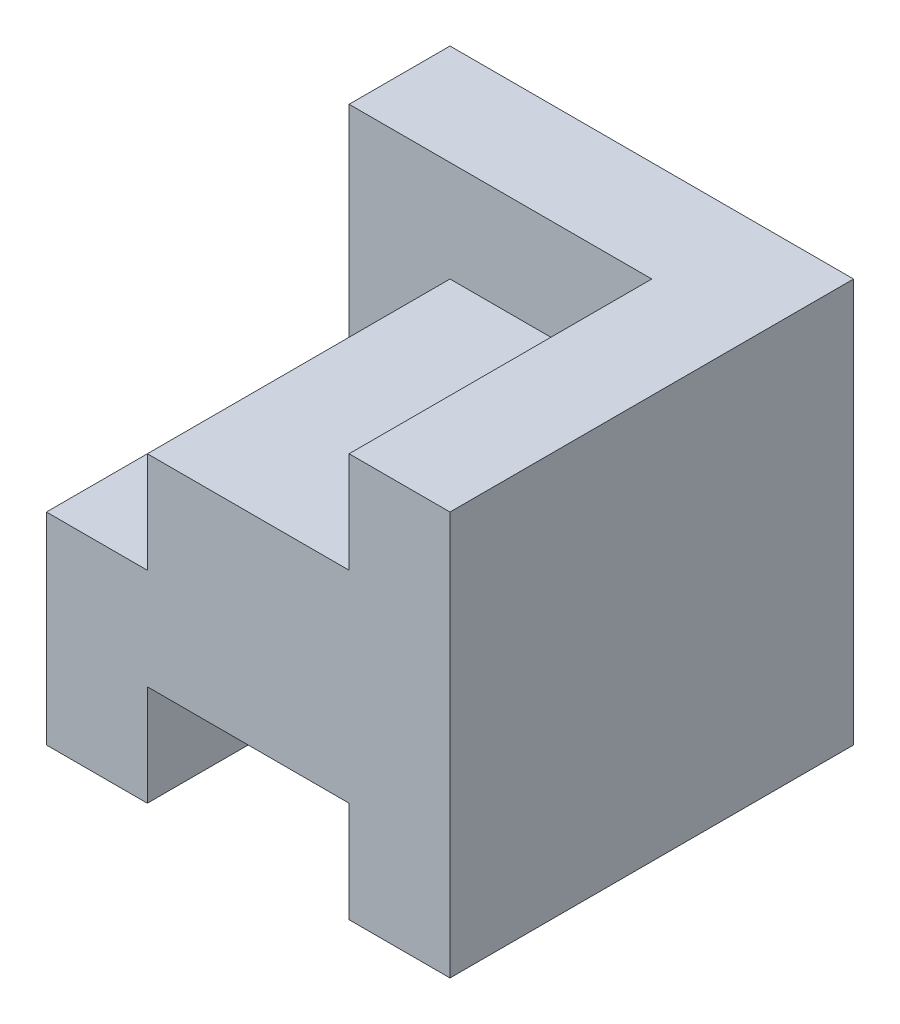
SolidWorks part; units mm, degrees
ref_plane "Front" through (0, 0, 0) normal (0, 0, 1) x (1, 0, 0)
ref_plane "Top" through (0, 0, 0) normal (0, 1, 0) x (1, 0, 0)
ref_plane "Right" through (0, 0, 0) normal (1, 0, 0) x (0, 0, -1)
sketch "Sketch1" plane through (0, 0, 0) normal (0, 0, 1) x (1, 0, 0)
  line L0 (0, 0) -> (0, 2)
  line L1 (0, 2) -> (1, 2)
  line L2 (1, 2) -> (1, 3)
  line L3 (1, 3) -> (3, 3)
  line L4 (3, 3) -> (3, 4)
  line L5 (3, 4) -> (4, 4)
  line L6 (4, 4) -> (4, 0)
  line L7 (4, 0) -> (3, 0)
  line L8 (3, 0) -> (3, 1)
  line L9 (3, 1) -> (1, 1)
  line L10 (1, 1) -> (1, 0)
  line L11 (1, 0) -> (0, 0)
  dimension "D1" = 4
  dimension "D2" = 1
  dimension "D3" = 1
  dimension "D4" = 1
  dimension "D5" = 1
  dimension "D6" = 2
  dimension "D7" = 1
  dimension "D8" = 1
  dimension "D9" = 2
extrude "Boss-Extrude1" add sketch "Sketch1" along normal blind 4
sketch "Sketch5" plane through (0, 0, 0) normal (0, 0, -1) x (-1, 0, 0)
  line L1 (0, 2) -> (-3, 2)
  line L2 (0, 2) -> (0, 4)
  line L3 (0, 4) -> (-3, 4)
  line L4 (-3, 2) -> (-3, 4)
extrude "Boss-Extrude3" add sketch "Sketch5" against normal blind 1
